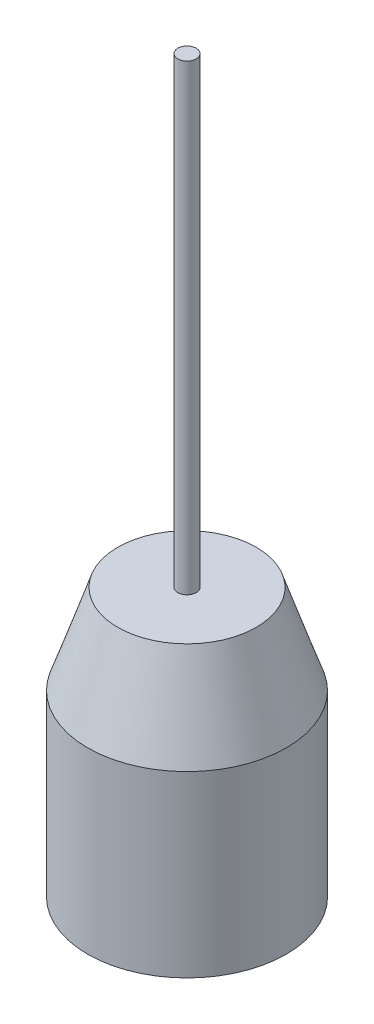
SolidWorks part; units mm, degrees
ref_plane "Front Plane" through (0, 0, 0) normal (0, 0, 1) x (1, 0, 0)
ref_plane "Top Plane" through (0, 0, 0) normal (0, 1, 0) x (1, 0, 0)
ref_plane "Right Plane" through (0, 0, 0) normal (1, 0, 0) x (0, 0, -1)
sketch "Sketch1" plane through (0, 0, 0) normal (0, 0, 1) x (1, 0, 0)
  line L0 (0, 0) -> (0, 58)
  line L1 (0, 58) -> (15, 58)
  line L2 (15, 58) -> (21.5, 38.6667)
  line L3 (21.5, 38.6667) -> (21.5, 0)
  line L4 (21.5, 0) -> (0, 0)
  line L5 (0, 58) -> (2, 58)
  line L6 (2, 58) -> (2, 158)
  line L7 (2, 158) -> (0, 158)
  line L8 (0, 158) -> (0, 58)
  dimension "D5" = 100
  dimension "D1" = 58
  dimension "D2" = 21.5
  dimension "D3" = 38.6667
  dimension "D4" = 15
revolve "Revolve1" add sketch "Sketch1" angle 360 about L0
hole_wizard "1/2-20 Tapped Hole1" positions "Sketch4" profile "Sketch3" tap size "1/2-20" standard "ANSI Inch"
sketch "Sketch4" plane through (0, 0, 0) normal (0, -1, 0) x (-1, 0, 0)
  point P0 (0, 0)
sketch "Sketch3" plane through (0, 0, 0) normal (1, 0, 0) x (0, 0, -1)
  line L0 (0, 0) -> (0, 33.4576)
  line L1 (0, 33.4576) -> (5.7544, 30)
  line L2 (5.7544, 30) -> (5.7544, 1.2306)
  line L3 (5.7544, 1.2306) -> (6.985, 0)
  line L5 (6.985, 0) -> (0, 0)
  line L6 (-5.7544, 1.2306) -> (-6.985, 0) construction
  line L10 (0, 33.4576) -> (-5.7544, 30) construction
  line L11 (0, -6.35) -> (0, 107.95) construction
  dimension "Tap Drill Dia." = 11.5087
  dimension "Tap Drill Depth" = 30
  dimension "Near C'Sink Dia." = 13.97
  dimension "Near C'Sink Angle" = 90
  dimension "Drill Angle" = 118
cosmetic thread "Hole Thread1"
